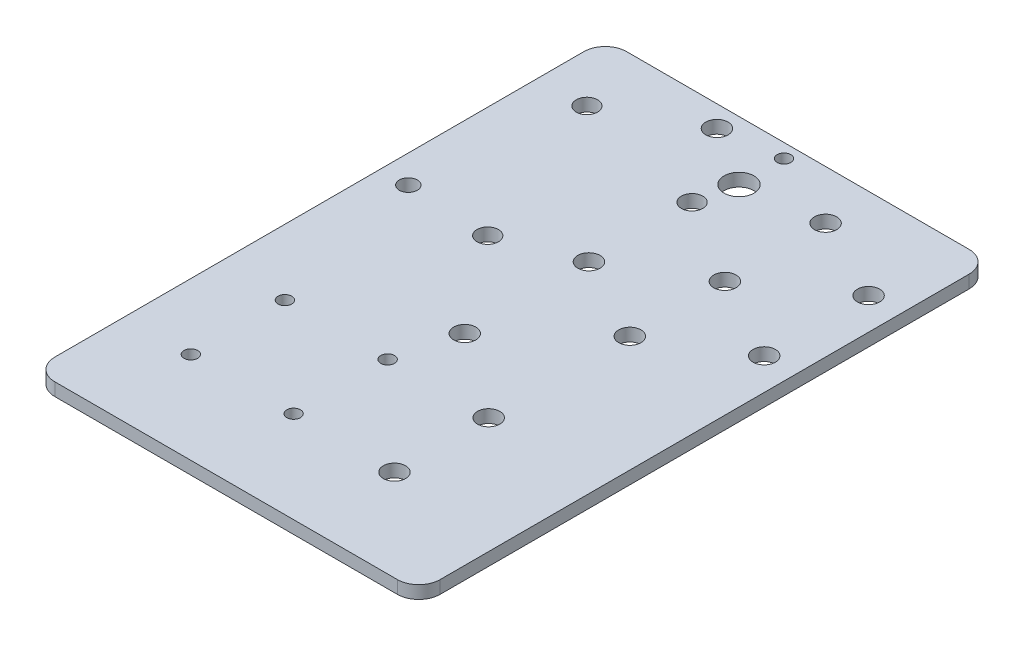
SolidWorks part; units mm, degrees
material "6061 合金"
ref_plane "前视基准面" through (0, 0, 0) normal (0, 0, 1) x (1, 0, 0)
ref_plane "上视基准面" through (0, 0, 0) normal (0, 1, 0) x (1, 0, 0)
ref_plane "右视基准面" through (0, 0, 0) normal (1, 0, 0) x (0, 0, -1)
sketch "草图1" plane through (0, 0, 0) normal (0, 1, 0) x (1, 0, 0)
  line L0 (-7.5, -1000) -> (-7.5, 49000) construction
  line L1 (-17.5, -35) -> (17.5, -35)
  line L2 (-17.5, -35) -> (-17.5, 35)
  line L3 (-17.5, 35) -> (17.5, 35)
  line L4 (17.5, -35) -> (17.5, 35)
  line L5 (0, 35) -> (0, -35) construction
  line L6 (-17.5, 0) -> (17.5, 0) construction
  circle A0 centre (-7.5, 22.5) radius 2.6
  circle A1 centre (-7.5, 0) radius 2.6
  circle A2 centre (-7.5, -22.5) radius 2.6
  circle A3 centre (-7.5, 10) radius 2.6
  circle A4 centre (-7.5, -10) radius 2.6
  point P0 (0, 0)
  dimension "D1" = 45
  dimension "D2" = 5.2
  dimension "D4" = 22.5
  dimension "D8" = 20
  dimension "D5" = 10
  dimension "D6" = 70
  dimension "D7" = 35
  dimension "D3" = 3
extrude "主板" add sketch "草图1" along normal blind 3
sketch "草图2" plane through (0, 3, 0) normal (0, 1, 0) x (1, 0, 0)
  line L0 (-1000, 0) -> (49000, 0) construction
  circle A0 centre (10, 0) radius 2.1
  dimension "D1" = 4.2
  dimension "D2" = 10
extrude "M4铝柱" cut sketch "草图2" against normal blind 3
sketch "草图3" plane through (0, 3, 0) normal (0, 1, 0) x (1, 0, 0)
  circle A0 centre (-7.5, 0) radius 2.6 construction
  circle A1 centre (-7.5, 0) radius 2.6 construction
  circle A2 centre (-7.5, -10) radius 2.6 construction
  circle A3 centre (-7.5, 10) radius 2.6 construction
  circle A4 centre (-7.5, -10) radius 2.6
  circle A5 centre (-7.5, 10) radius 2.6
extrude "填补" add sketch "草图3" against normal through all
sketch "草图4" plane through (0, 3, 0) normal (0, 1, 0) x (1, 0, 0)
  line L1 (-7.5, -22.5) -> (10, -22.5) construction
  line L2 (-7.5, -22.5) -> (-7.5, 22.5) construction
  line L3 (-7.5, 22.5) -> (10, 22.5) construction
  line L4 (10, -22.5) -> (10, 22.5) construction
  line L5 (1.25, 22.5) -> (1.25, -22.5) construction
  line L6 (-7.5, 0) -> (10, 0) construction
  circle A0 centre (-7.5, 22.5) radius 2.6 construction
  circle A1 centre (10, 0) radius 2.1 construction
  circle A2 centre (10, 22.5) radius 2.1
  circle A3 centre (10, -22.5) radius 2.1
  point P0 (1.25, 0)
extrude "摩擦轮垫板" cut sketch "草图4" against normal through all
sketch "草图5" plane through (0, 3, 0) normal (0, 1, 0) x (1, 0, 0)
  line L0 (17.5, 35) -> (-17.5, 35) construction
  line L1 (17.5, -35) -> (66.5, -35) construction
  line L2 (17.5, -35) -> (17.5, 35) construction
  line L3 (17.5, 35) -> (66.5, 35) construction
  line L4 (66.5, -35) -> (66.5, 35) construction
  line L5 (0, -1000) -> (0, 49000) construction
  line L6 (-17.5, 35) -> (-66.5, 35)
  line L7 (-66.5, -35) -> (-66.5, 35)
  line L8 (-17.5, -35) -> (-66.5, -35)
  line L9 (-17.5, -35) -> (-17.5, 35)
  dimension "D1" = 49
extrude "EXTRA" add sketch "草图5" against normal through all
fillet "圆角5" [suppressed] radius 5
sketch "草图6" plane through (0, 3, 0) normal (0, 1, 0) x (1, 0, 0)
  line L0 (-999.7092, 0) -> (49000.2908, 0) construction
  line L2 (-40.5, -989.9006) -> (-40.5, 49010.0994) construction
  line L3 (-7.5, -977.5) -> (-7.5, 49022.5) construction
  circle A0 centre (-44.5, 0) radius 2.1
  circle A1 centre (-36.5, 0) radius 2.1
  dimension "D1" = 4.2
  dimension "D3" = 8
  dimension "D2" = 33
extrude "垂直板接件" cut sketch "草图6" against normal blind 10
sketch "草图7" plane through (0, 3, 0) normal (0, 1, 0) x (1, 0, 0)
  line L0 (-1000, 0) -> (49000, 0) construction
  line L1 (0, -1000) -> (0, 49000) construction
  circle A0 centre (-60, 17.5) radius 2.1
  circle A1 centre (-60, 17.5) radius 5 construction
  circle A2 centre (-60, -17.5) radius 2.1
  dimension "D1" = 4.2
  dimension "D2" = 10
  dimension "D4" = 60
  dimension "D3" = 35
extrude "ETRA铝柱" cut sketch "草图7" against normal blind 10
sketch "草图8" [suppressed] plane through (0, 3, 0) normal (0, 1, 0) x (1, 0, 0)
  line L0 (-17.5, 30) -> (-17.5, -30) construction
  line L1 (17.5, 30) -> (-17.5, 30)
  line L2 (17.5, 30) -> (17.5, 55)
  line L3 (17.5, 55) -> (-17.5, 55)
  line L4 (-17.5, 30) -> (-17.5, 55)
  line L5 (0, -1000) -> (0, 49000) construction
  line L6 (-1000, 0) -> (49000, 0) construction
  line L7 (17.5, -55) -> (-17.5, -55)
  line L8 (-17.5, -30) -> (-17.5, -55)
  line L9 (17.5, -30) -> (-17.5, -30)
  line L10 (17.5, -30) -> (17.5, -55)
  dimension "D1" = 110
extrude "ETRA2" [suppressed] add sketch "草图8" against normal through all
sketch "草图9" [suppressed] plane through (0, 3, 0) normal (0, 1, 0) x (1, 0, 0)
  line L0 (-1000.6559, 0) -> (48999.3441, 0) construction
  line L1 (0, -1000) -> (0, 49000) construction
  line L2 (-7.5, -977.5) -> (-7.5, 49022.5) construction
  line L3 (10, -1000) -> (10, 49000) construction
  circle A0 centre (-7.5, 0) radius 2.6
  circle A1 centre (-7.5, -22.5) radius 2.6 construction
  circle A2 centre (-7.5, 45) radius 2.6
  circle A3 centre (-7.5, -45) radius 2.6
  circle A4 centre (10, 45) radius 2.1
  circle A5 centre (10, 0) radius 2.1 construction
  circle A6 centre (10, -45) radius 2.1
  dimension "D1" = 2
  dimension "D2" = 90
  dimension "D3" = 90
extrude "ETRA2铝柱" [suppressed] cut sketch "草图9" against normal blind 10
sketch "草图10" plane through (0, 0, 0) normal (0, -1, 0) x (1, 0, 0)
  line L0 (-66.5, 35) -> (17.5, 35) construction
  line L1 (-21.5, 31.75) -> (-43.5, 31.75) construction
  line L2 (-21.5, 31.75) -> (-21.5, 21.25) construction
  line L3 (-21.5, 21.25) -> (-43.5, 21.25) construction
  line L4 (-43.5, 31.75) -> (-43.5, 21.25) construction
  line L5 (-32.5, 21.25) -> (-32.5, 31.75) construction
  line L6 (-21.5, 26.5) -> (-43.5, 26.5) construction
  line L7 (-18.5, 18.5) -> (-46.5, 18.5) construction
  line L8 (-18.5, 18.5) -> (-18.5, 34.5) construction
  line L9 (-18.5, 34.5) -> (-46.5, 34.5) construction
  line L10 (-46.5, 18.5) -> (-46.5, 34.5) construction
  line L11 (-32.5, 34.5) -> (-32.5, 18.5) construction
  line L12 (-18.5, 26.5) -> (-46.5, 26.5) construction
  line L13 (-66.5, 35) -> (17.5, 35) construction
  line L14 (-40.5, -998.1832) -> (-40.5, 49001.8168) construction
  line L16 (-1000, 0) -> (49000, 0) construction
  circle A0 centre (-43.5, -21.25) radius 1.6
  circle A1 centre (-21.5, -21.25) radius 1.6 construction
  circle A2 centre (-21.5, -31.75) radius 1.6
  circle A3 centre (-43.5, -31.75) radius 1.6
  circle A4 centre (-60, 17.5) radius 5 construction
  circle A5 centre (-36.5, 0) radius 2.1 construction
  circle A6 centre (-44.5, 0) radius 2.1 construction
  circle A7 centre (-43.5, 21.25) radius 1.6
  circle A8 centre (-21.5, 31.75) radius 1.6
  circle A9 centre (-43.5, 31.75) radius 1.6
  circle A10 centre (-21.5, 21.25) radius 1.6 construction
  circle A11 centre (-21.5, 21.25) radius 3.5
  circle A12 centre (-21.5, -21.25) radius 3.5
  point P0 (-32.5, 26.5)
  point P4 (-32.5, 26.5)
  dimension "D5" = 10
  dimension "D7" = 3.2
  dimension "D8" = 0.5
  dimension "D9" = 7
  dimension "D1" = 22
  dimension "D2" = 10.5
  dimension "D3" = 28
  dimension "D4" = 16
  dimension "D6" = 8
extrude "限位开关" cut sketch "草图10" against normal through all
fillet "圆角5.0" radius 5 4 edges at (17.5, 1.5, -35) (-66.5, 1.5, -35) (17.5, 1.5, 35) (-66.5, 1.5, 35)
fillet "圆角5.1" [suppressed] radius 5
sketch "草图12" plane through (0, 3, 0) normal (0, 1, 0) x (1, 0, 0)
  circle A0 centre (-36.5, 0) radius 2.1
  circle A1 centre (-44.5, 0) radius 2.1
extrude "凸台-拉伸1" add sketch "草图12" against normal up to surface (3 mm away) up to face at (-21.5, 0, 30.15)
sketch "草图13" plane through (0, 3, 0) normal (0, 1, 0) x (1, 0, 0)
  circle A0 centre (-52.5, 0) radius 1.5
  circle A1 centre (-28.5, 0) radius 1.5
extrude "切除-拉伸1" cut sketch "草图13" against normal through all
sketch "草图14" plane through (0, 3, 0) normal (0, 1, 0) x (1, 0, 0)
  circle A0 centre (-28.5, 0) radius 1.5
extrude "凸台-拉伸2" add sketch "草图14" against normal blind 3
sketch "草图15" plane through (0, 3, 0) normal (0, 1, 0) x (1, 0, 0)
  circle A0 centre (-23.3937, 12.1665) radius 2.5
  circle A1 centre (-23.3937, -11.9198) radius 2.5
extrude "切除-拉伸2" cut sketch "草图15" against normal through all
sketch "草图16" plane through (0, 3, 0) normal (0, 1, 0) x (1, 0, 0)
  circle A0 centre (-7.5, 22.5) radius 2.6
  circle A1 centre (-7.5, 0) radius 2.6
  circle A2 centre (-7.5, -22.5) radius 2.6
extrude "凸台-拉伸3" add sketch "草图16" against normal blind 3
sketch "草图18" plane through (0, 0, 0) normal (0, -1, 0) x (1, 0, 0)
  circle A0 centre (-3.5588, 0) radius 2.5
  circle A1 centre (-3.5588, 22.2023) radius 2.5
  circle A2 centre (-3.5588, -23.5188) radius 2.5
extrude "切除-拉伸3" cut sketch "草图18" against normal blind 3
sketch "草图19" plane through (0, 0, 0) normal (0, -1, 0) x (1, 0, 0)
  circle A0 centre (-43.5, 21.25) radius 2.1808
  circle A1 centre (-43.5, 31.75) radius 1.6618
extrude "凸台-拉伸4" add sketch "草图19" against normal blind 3
sketch "草图20" plane through (0, 3, 0) normal (0, 1, 0) x (1, 0, 0)
  circle A0 centre (-40.5, 1.5519) radius 2.5
  circle A1 centre (-40.5, -18.4481) radius 2.5
extrude "切除-拉伸4" cut sketch "草图20" against normal through all
sketch "草图21" plane through (0, 3, 0) normal (0, 1, 0) x (1, 0, 0)
  circle A0 centre (-43.5, 21.25) radius 2.4555
  circle A1 centre (-43.5, 31.75) radius 2.5446
extrude "凸台-拉伸5" add sketch "草图21" against normal blind 3
sketch "草图22" plane through (0, 3, 0) normal (0, 1, 0) x (1, 0, 0)
  circle A0 centre (-40.5, 25) radius 2.5
extrude "切除-拉伸5" cut sketch "草图22" against normal through all
sketch "草图23" plane through (0, 3, 0) normal (0, 1, 0) x (1, 0, 0)
  circle A0 centre (-40.5, 1.5519) radius 3.6098
extrude "凸台-拉伸7" add sketch "草图23" against normal blind 3
sketch "草图24" plane through (0, 3, 0) normal (0, 1, 0) x (1, 0, 0)
  circle A0 centre (-39.1537, 2.8663) radius 2.5
extrude "切除-拉伸6" cut sketch "草图24" against normal through all
sketch "草图25" plane through (0, 3, 0) normal (0, 1, 0) x (1, 0, 0)
  line L0 (12.5, 35) -> (17.5, 35)
  line L1 (17.5, 35) -> (23.5, 35)
  line L2 (23.5, 35) -> (23.5, -35)
  line L3 (23.5, -35) -> (12.5, -35)
  line L4 (12.5, -35) -> (12.5, 35)
  arc A0 (12.5, -35) -> (17.5, -30) centre (12.5, -30) ccw construction
extrude "凸台-拉伸8" add sketch "草图25" against normal blind 3
fillet "圆角6" radius 5 2 edges at (23.5, 1.5, 35) (23.5, 1.5, -35)
sketch "草图26" plane through (0, 0, 0) normal (0, -1, 0) x (1, 0, 0)
  circle A0 centre (10, 22.5) radius 2.1
  circle A1 centre (10, 0) radius 2.1
  circle A2 centre (10, -22.5) radius 2.1
extrude "凸台-拉伸9" add sketch "草图26" against normal blind 3
sketch "草图27" plane through (0, 3, 0) normal (0, 1, 0) x (1, 0, 0)
  circle A0 centre (16.0863, -10.4652) radius 2.5
  circle A1 centre (16.0863, 13.9085) radius 2.5
extrude "切除-拉伸7" cut sketch "草图27" against normal through all
sketch "草图28" plane through (0, 3, 0) normal (0, 1, 0) x (1, 0, 0)
  circle A0 centre (-39.1537, 2.8663) radius 2.3782
  circle A1 centre (-40.5, 25) radius 2.5
  dimension "D1" = 4.7565
  dimension "D2" = 5
extrude "凸台-拉伸10" add sketch "草图28" against normal up to surface (3 mm away) up to face at (16.0863, 0, 12.9652)
sketch "草图29" plane through (0, 3, 0) normal (0, 1, 0) x (1, 0, 0)
  circle A0 centre (-39.1537, 2.8663) radius 3.1047
  dimension "D1" = 6.2094
extrude "凸台-拉伸11" add sketch "草图29" against normal up to surface (3 mm away) up to face at (16.0863, 0, 12.9652)
sketch "草图30" plane through (0, 3, 0) normal (0, 1, 0) x (1, 0, 0)
  circle A0 centre (-35.4137, 30) radius 2.5
  dimension "D1" = 5
extrude "切除-拉伸8" cut sketch "草图30" against normal through all
sketch "草图31" plane through (0, 0, 0) normal (0, -1, 0) x (1, 0, 0)
  circle A0 centre (-52.5, 0) radius 1.5
  circle A1 centre (-60, -17.5) radius 2.1
extrude "凸台-拉伸12" add sketch "草图31" against normal up to surface (3 mm away) up to face at (-35.4137, 3, -27.5)
sketch "草图32" plane through (0, 3, 0) normal (0, 1, 0) x (1, 0, 0)
  line L0 (-63.6537, 19.3704) -> (-46.6537, 19.3704) construction
  line L1 (-63.6537, 676.8668) -> (-63.6537, 1.7596) construction
  line L2 (-46.6537, 676.8668) -> (-46.6537, 1.7596) construction
  circle A0 centre (-55.1537, 19.3704) radius 2.5
extrude "切除-拉伸9" cut sketch "草图32" against normal through all
sketch "草图33" plane through (0, 3, 0) normal (0, 1, 0) x (1, 0, 0)
  line L0 (-66.5, -30) -> (-64.6199, -98.5583)
  line L1 (-59.646, -98.3839) -> (-69.5938, -98.7327) construction
  line L2 (-66.5, -30) -> (23.5, -24.4961)
  line L4 (23.5, -30) -> (23.5, 30) construction
  line L5 (156.3463, -24.4961) -> (6.3463, -24.4961) construction
  line L6 (23.5, -24.4961) -> (28.0292, -98.5583)
  line L7 (28.0292, -98.5583) -> (-64.6199, -98.5583)
extrude "凸台-拉伸13" add sketch "草图33" against normal up to surface (3 mm away)
sketch "草图34" plane through (0, 3, 0) normal (0, 1, 0) x (1, 0, 0)
  line L0 (-66.5, -30) -> (-66.5, -98.6242)
  line L1 (-59.646, -98.3839) -> (-69.5938, -98.7327) construction
  line L2 (-66.5, -98.6242) -> (-64.6199, -98.5583)
  line L3 (-64.6199, -98.5583) -> (-66.5, -30)
extrude "凸台-拉伸15" add sketch "草图34" against normal up to surface (3 mm away) up to face at (-25.8906, 0, 9.5345)
sketch "草图35" plane through (0, 3, 0) normal (0, 1, 0) x (1, 0, 0)
  line L0 (23.5, -24.4961) -> (23.5, -98.5583)
  line L1 (-64.6199, -98.5583) -> (28.0292, -98.5583) construction
  line L2 (23.5, -98.5583) -> (28.7587, -98.5583)
  line L3 (28.7587, -98.5583) -> (23.5, -24.4961)
extrude "切除-拉伸10" cut sketch "草图35" against normal through all
sketch "草图37" plane through (0, 3, 0) normal (0, 1, 0) x (1, 0, 0)
  circle A0 centre (-51.1537, -77.1337) radius 1.5
  circle A1 centre (-27.1537, -77.1337) radius 1.5
extrude "切除-拉伸11" cut sketch "草图37" against normal through all
sketch "草图38" plane through (0, 3, 0) normal (0, 1, 0) x (1, 0, 0)
  circle A0 centre (-51.1537, -55.1337) radius 1.5
  circle A1 centre (-27.1537, -55.1337) radius 1.5
extrude "切除-拉伸12" cut sketch "草图38" against normal through all
sketch "草图39" plane through (0, 3, 0) normal (0, 1, 0) x (1, 0, 0)
  circle A0 centre (-21.5, -21.25) radius 3.5
extrude "凸台-拉伸16" add sketch "草图39" against normal up to surface (3 mm away) up to face at (-51.1537, 0, 56.6337)
fillet "圆角7" radius 5 2 edges at (23.5, 1.5, 98.5583) (-66.5, 1.5, 98.6242)
sketch "草图42" plane through (0, 3, 0) normal (0, 1, 0) x (1, 0, 0)
  circle A0 centre (-3.5588, 23.5188) radius 2.6
  circle A1 centre (-3.5588, 0) radius 2.6
  circle A2 centre (-3.5588, -22.2023) radius 2.6
  circle A3 centre (-3.5588, -55.1695) radius 2.6
  circle A4 centre (-3.5588, -77.1695) radius 2.6
  circle A5 centre (-23.3937, -11.9198) radius 2.6
  circle A6 centre (-23.3937, -40.9198) radius 2.6
  circle A7 centre (-35.4137, 30) radius 2.6
  circle A8 centre (16.0863, 13.9085) radius 2.6
  circle A9 centre (16.0863, -10.4652) radius 2.6
  circle A10 centre (-51.1537, -77.1337) radius 1.6
  circle A11 centre (-27.1537, -77.1337) radius 1.6
  circle A12 centre (-27.1537, -55.1695) radius 1.6
  circle A13 centre (-51.1537, -55.1695) radius 1.6
  point P13 (-31.2242, -77.1337)
  point P14 (-31.9151, -77.2918)
  point P15 (-27.1537, -77.1337)
  point P25 (-28.8981, -71.5664)
  point P28 (-31.6326, -54.4341)
  point P37 (-47.8716, -54.8232)
  point P38 (-27.1537, -55.1695)
  point P39 (-51.1537, -55.1695)
  point P45 (-27.1537, -55.1695)
  point P46 (-51.1537, -55.1695)
  dimension "D1" = 29
extrude "切除-拉伸13" cut sketch "草图42" against normal blind 10
